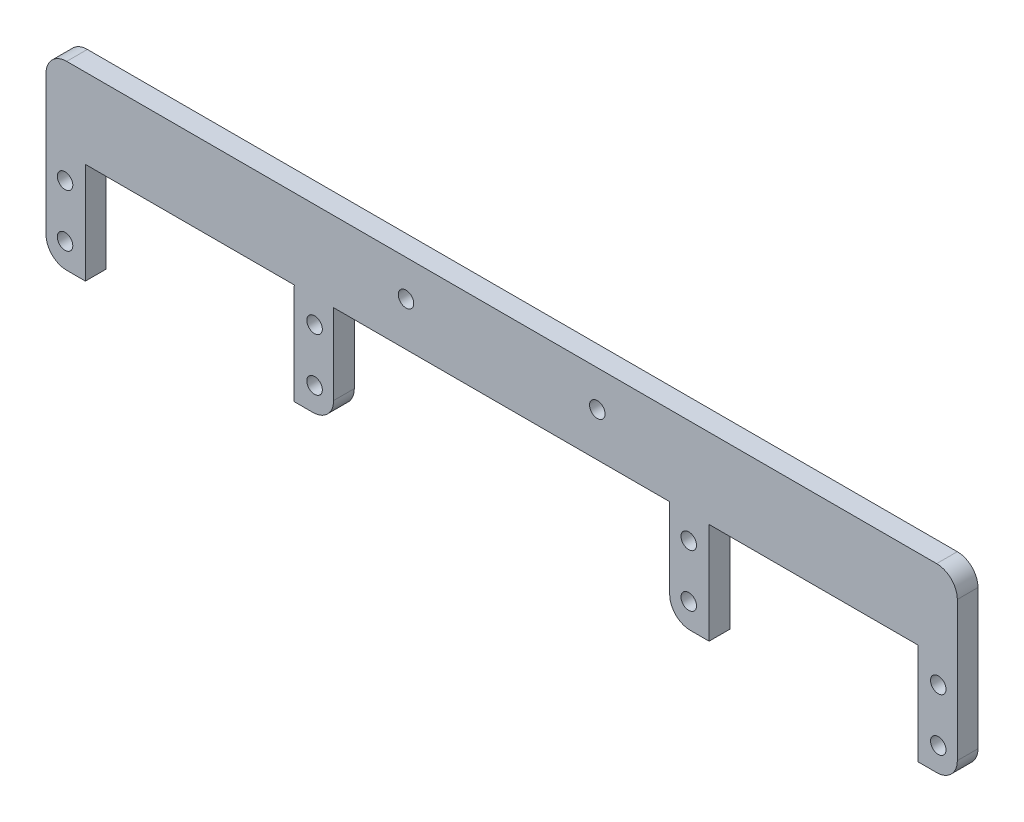
SolidWorks part; units mm, degrees
material "Acrylic (Medium-high impact)"
ref_plane "Front Plane" through (0, 0, 0) normal (0, 0, 1) x (1, 0, 0)
ref_plane "Top Plane" through (0, 0, 0) normal (0, 1, 0) x (1, 0, 0)
ref_plane "Right Plane" through (0, 0, 0) normal (1, 0, 0) x (0, 0, -1)
sketch "Sketch2" plane through (0, 0, 0) normal (0, 0, 1) x (1, 0, 0)
  line L0 (-87.0811, 16.9235) -> (-46.6951, 16.9235)
  line L1 (-46.6951, 16.9235) -> (-46.6951, -2.6345)
  line L2 (-46.6951, -2.6345) -> (-39.0751, -2.6345)
  line L3 (-39.0751, -2.6345) -> (-39.0751, 32.3655)
  line L4 (-39.0751, 32.3655) -> (-67.0811, 32.3655)
  line L5 (-207.7071, 16.9235) -> (-167.2319, 16.7363)
  line L6 (-94.7011, 16.9235) -> (-94.7011, -2.6345)
  line L7 (-94.7011, -2.6345) -> (-87.0811, -2.6345)
  line L8 (-87.0811, -2.6345) -> (-87.0811, 16.9235)
  line L9 (-87.0811, 16.9235) -> (-87.1703, 16.7363)
  line L10 (-74.7011, 32.3655) -> (-67.0811, 32.3655)
  line L11 (-159.7011, 16.9235) -> (-94.7011, 16.9235)
  line L12 (-167.3211, 32.3655) -> (-159.7011, 32.3655)
  line L13 (-167.3211, 16.9235) -> (-167.2319, 16.7363)
  line L14 (-167.3211, -2.6345) -> (-167.3211, 16.9235)
  line L15 (-159.7011, -2.6345) -> (-167.3211, -2.6345)
  line L16 (-159.7011, 16.9235) -> (-159.7011, -2.6345)
  line L18 (-215.3271, 32.3655) -> (-167.3211, 32.3655)
  line L19 (-215.3271, -2.6345) -> (-215.3271, 32.3655)
  line L20 (-207.7071, -2.6345) -> (-215.3271, -2.6345)
  line L21 (-207.7071, 16.9235) -> (-207.7071, -2.6345)
  line L22 (-167.3211, 16.9235) -> (-207.7071, 16.9235)
  line L23 (-159.7011, 32.3655) -> (-74.7011, 32.3655)
extrude "Boss-Extrude2" add sketch "Sketch2" along normal blind 4
fillet "Fillet1" radius 4 6 edges at (-94.7011, -2.6345, 2) (-159.7011, -2.6345, 2) (-215.3271, -2.6345, 2) (-39.0751, -2.6345, 2) (-215.3271, 32.3655, 2) (-39.0751, 32.3655, 2)
sketch "Sketch3" plane through (0, 0, 4) normal (0, 0, 1) x (1, 0, 0)
  line L0 (-211.3271, 32.3655) -> (-43.0751, 32.3655) construction
  line L2 (-159.7011, 16.9235) -> (-159.7011, 1.3655) construction
  line L4 (-94.7011, 16.9235) -> (-94.7011, 1.3655) construction
  circle A0 centre (-145.7011, 25.3655) radius 1.5
  circle A1 centre (-108.7011, 25.3655) radius 1.5
  dimension "D1" = 7
  dimension "D2" = 14
  dimension "D3" = 14
  dimension "D4" = 7
sketch "Sketch6" plane through (0, 0, 4) normal (0, 0, 1) x (1, 0, 0)
  line L1 (-167.3211, 16.9235) -> (-207.7071, 16.9235) construction
  line L2 (-207.7071, 16.9235) -> (-207.7071, -2.6345) construction
  circle A0 centre (-211.6441, 12.2245) radius 1.5
  circle A1 centre (-163.3841, 12.2245) radius 1.5
  circle A2 centre (-163.3841, 2.0645) radius 1.5
  circle A3 centre (-211.6441, 2.0645) radius 1.5
  circle A4 centre (-91.0181, 12.2245) radius 1.5
  circle A5 centre (-42.7581, 12.2245) radius 1.5
  circle A6 centre (-42.7581, 2.0645) radius 1.5
  circle A7 centre (-91.0181, 2.0645) radius 1.5
  dimension "D1" = 4.699
  dimension "D2" = 3.937
  dimension "D5" = 48.26
  dimension "D6" = 10.16
  dimension "D9" = 72.366
  dimension "D3" = 2
  dimension "D4" = 2
  dimension "D7" = 2
  dimension "D8" = 2
extrude "Cut-Extrude1" cut sketch "Sketch6" against normal blind 4
extrude "Cut-Extrude2" cut sketch "Sketch3" against normal blind 4 contours A0 | A1
